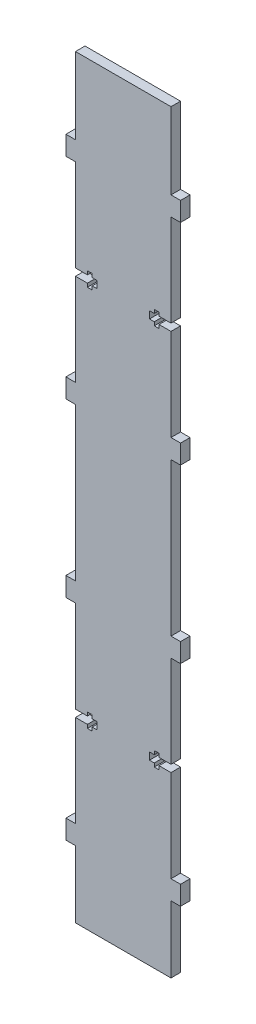
SolidWorks part; units mm, degrees
ref_plane "Front Plane" through (0, 0, 0) normal (0, 0, 1) x (1, 0, 0)
ref_plane "Top Plane" through (0, 0, 0) normal (0, 1, 0) x (1, 0, 0)
ref_plane "Right Plane" through (0, 0, 0) normal (1, 0, 0) x (0, 0, -1)
sketch "Sketch1" plane through (0, 0, 0) normal (0, 0, 1) x (1, 0, 0)
  line L0 (76.2, 190.5) -> (76.2, 203.2)
  line L2 (6.35, 457.2) -> (6.35, 508)
  line L3 (6.35, 508) -> (69.85, 508)
  line L5 (6.35, 203.2) -> (6.35, 304.8)
  line L6 (0, 203.2) -> (6.35, 203.2)
  line L7 (0, 203.2) -> (0, 190.5)
  line L8 (0, 190.5) -> (6.35, 190.5)
  line L10 (0, 63.5) -> (6.35, 63.5)
  line L11 (0, 63.5) -> (0, 50.8)
  line L12 (0, 50.8) -> (6.35, 50.8)
  line L15 (6.35, 63.5) -> (6.35, 190.5)
  line L16 (6.35, 50.8) -> (6.35, 6.35)
  line L17 (6.35, 6.35) -> (69.85, 6.35)
  line L18 (0, 304.8) -> (0, 317.5)
  line L19 (6.35, 444.5) -> (6.35, 317.5)
  line L20 (0, 457.2) -> (0, 444.5)
  line L21 (0, 457.2) -> (6.35, 457.2)
  line L23 (0, 444.5) -> (6.35, 444.5)
  line L25 (0, 317.5) -> (6.35, 317.5)
  line L27 (0, 304.8) -> (6.35, 304.8)
  line L29 (76.2, 50.8) -> (76.2, 63.5)
  line L30 (76.2, 444.5) -> (76.2, 457.2)
  line L31 (76.2, 304.8) -> (69.85, 304.8)
  line L32 (76.2, 304.8) -> (76.2, 317.5)
  line L33 (76.2, 317.5) -> (69.85, 317.5)
  line L35 (76.2, 444.5) -> (69.85, 444.5)
  line L37 (76.2, 457.2) -> (69.85, 457.2)
  line L39 (69.85, 444.5) -> (69.85, 317.5)
  line L41 (69.85, 50.8) -> (69.85, 6.35)
  line L42 (69.85, 63.5) -> (69.85, 190.5)
  line L43 (69.85, 304.8) -> (69.85, 203.2)
  line L45 (76.2, 50.8) -> (69.85, 50.8)
  line L47 (76.2, 63.5) -> (69.85, 63.5)
  line L49 (76.2, 190.5) -> (69.85, 190.5)
  line L51 (76.2, 203.2) -> (69.85, 203.2)
  line L53 (69.85, 457.2) -> (69.85, 508)
  point P21 (6.35, 254)
  point P46 (69.85, 254)
  dimension "D5" = 12.7
  dimension "D6" = 12.7
  dimension "D7" = 6.35
  dimension "D8" = 6.35
extrude "Boss-Extrude1" add sketch "Sketch1" along normal blind 6.35
sketch "Sketch2" plane through (0, 0, 0) normal (0, 0, -1) x (-1, 0, 0)
  line L0 (-58.7375, 124.6188) -> (-55.5625, 124.6188)
  line L1 (-69.85, 190.5) -> (-76.2, 190.5) construction
  line L2 (-76.2, 63.5) -> (-69.85, 63.5) construction
  line L4 (-69.85, 203.2) -> (-69.85, 304.8) construction
  line L5 (-69.85, 124.6188) -> (-69.85, 129.3813)
  line L6 (-69.85, 129.3813) -> (-61.9125, 129.3813)
  line L7 (-69.85, 254) -> (-6.35, 254)
  line L8 (-6.35, 304.8) -> (-6.35, 203.2) construction
  line L9 (-38.1, 6.35) -> (-38.1, 254)
  line L10 (-6.35, 6.35) -> (-69.85, 6.35) construction
  line L11 (-6.35, 124.6188) -> (-14.2875, 124.6188)
  line L12 (-17.4625, 124.6188) -> (-17.4625, 122.2375)
  line L13 (-58.7375, 129.3813) -> (-58.7375, 131.7625)
  line L14 (-58.7375, 131.7625) -> (-61.9125, 131.7625)
  line L15 (-61.9125, 129.3813) -> (-61.9125, 131.7625)
  line L16 (-58.7375, 129.3813) -> (-55.5625, 129.3813)
  line L17 (-17.4625, 122.2375) -> (-14.2875, 122.2375)
  line L18 (-14.2875, 124.6188) -> (-14.2875, 122.2375)
  line L19 (-55.5625, 129.3813) -> (-55.5625, 124.6188)
  line L20 (-61.9125, 124.6188) -> (-61.9125, 122.2375)
  line L21 (-58.7375, 122.2375) -> (-61.9125, 122.2375)
  line L22 (-58.7375, 124.6188) -> (-58.7375, 122.2375)
  line L23 (-20.6375, 129.3812) -> (-20.6375, 124.6188)
  line L24 (-17.4625, 129.3812) -> (-20.6375, 129.3812)
  line L25 (-69.85, 124.6188) -> (-61.9125, 124.6188)
  line L26 (-14.2875, 129.3812) -> (-14.2875, 131.7625)
  line L27 (-17.4625, 131.7625) -> (-14.2875, 131.7625)
  line L28 (-17.4625, 129.3812) -> (-17.4625, 131.7625)
  line L29 (-6.35, 129.3812) -> (-14.2875, 129.3812)
  line L30 (-6.35, 124.6188) -> (-6.35, 129.3812)
  line L31 (-17.4625, 124.6188) -> (-20.6375, 124.6188)
  line L32 (-17.4625, 383.3813) -> (-20.6375, 383.3813)
  line L33 (-6.35, 383.3813) -> (-6.35, 378.6187)
  line L34 (-6.35, 378.6187) -> (-14.2875, 378.6187)
  line L35 (-17.4625, 378.6187) -> (-17.4625, 376.2375)
  line L36 (-17.4625, 376.2375) -> (-14.2875, 376.2375)
  line L37 (-14.2875, 378.6187) -> (-14.2875, 376.2375)
  line L38 (-69.85, 383.3812) -> (-61.9125, 383.3812)
  line L39 (-17.4625, 378.6187) -> (-20.6375, 378.6187)
  line L40 (-20.6375, 378.6187) -> (-20.6375, 383.3813)
  line L41 (-58.7375, 383.3812) -> (-58.7375, 385.7625)
  line L42 (-58.7375, 385.7625) -> (-61.9125, 385.7625)
  line L43 (-61.9125, 383.3812) -> (-61.9125, 385.7625)
  line L44 (-55.5625, 378.6187) -> (-55.5625, 383.3812)
  line L45 (-14.2875, 383.3813) -> (-14.2875, 385.7625)
  line L46 (-17.4625, 385.7625) -> (-14.2875, 385.7625)
  line L47 (-58.7375, 378.6187) -> (-55.5625, 378.6187)
  line L48 (-61.9125, 378.6187) -> (-61.9125, 376.2375)
  line L49 (-58.7375, 376.2375) -> (-61.9125, 376.2375)
  line L50 (-58.7375, 378.6187) -> (-58.7375, 376.2375)
  line L51 (-17.4625, 383.3813) -> (-17.4625, 385.7625)
  line L52 (-6.35, 383.3813) -> (-14.2875, 383.3813)
  line L53 (-69.85, 378.6187) -> (-61.9125, 378.6187)
  line L54 (-69.85, 383.3812) -> (-69.85, 378.6187)
  line L55 (-58.7375, 383.3812) -> (-55.5625, 383.3812)
  point P2 (-73.025, 190.5)
  point P6 (-73.025, 63.5)
  dimension "D1" = 127
  dimension "D3" = 2.3813
  dimension "D5" = 3.175
  dimension "D6" = 3.175
extrude "Cut-Extrude1" cut sketch "Sketch2" against normal blind 6.35 contours L38 L43 L42 L41 L55 L44 L47 L50 L49 L48 L53 L54 | L52 L45 L46 L51 L32 L40 L39 L35 L36 L37 L34 L33 | L22 L21 L20 L25 L5 L6 L15 L14 L13 L16 L19 L0 | L12 L17 L18 L11 L30 L29 L26 L27 L28 L24 L23 L31
